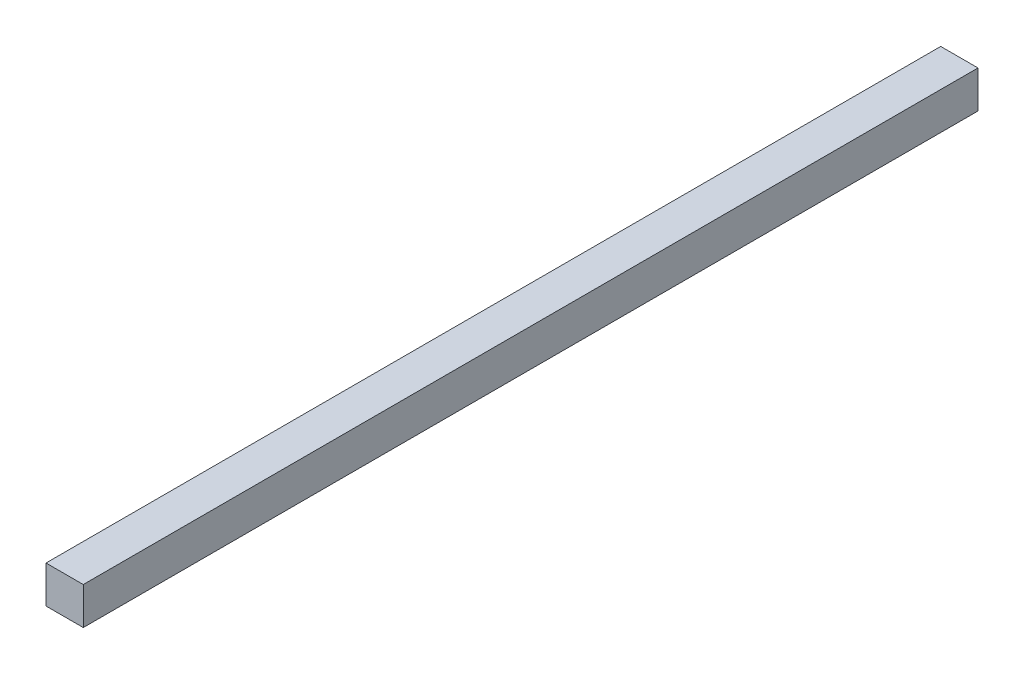
SolidWorks part; units mm, degrees
ref_plane "Front Plane" through (0, 0, 0) normal (0, 0, 1) x (1, 0, 0)
ref_plane "Top Plane" through (0, 0, 0) normal (0, 1, 0) x (1, 0, 0)
ref_plane "Right Plane" through (0, 0, 0) normal (1, 0, 0) x (0, 0, -1)
sketch "Sketch1" plane through (0, 0, 0) normal (0, 1, 0) x (1, 0, 0)
  line L1 (0, 0) -> (25.4, 0)
  line L2 (0, 0) -> (0, 609.6)
  line L3 (0, 609.6) -> (25.4, 609.6)
  line L4 (25.4, 0) -> (25.4, 609.6)
  dimension "D1" = 609.6
  dimension "D2" = 25.4
extrude "Boss-Extrude1" add sketch "Sketch1" along normal blind 25.4
